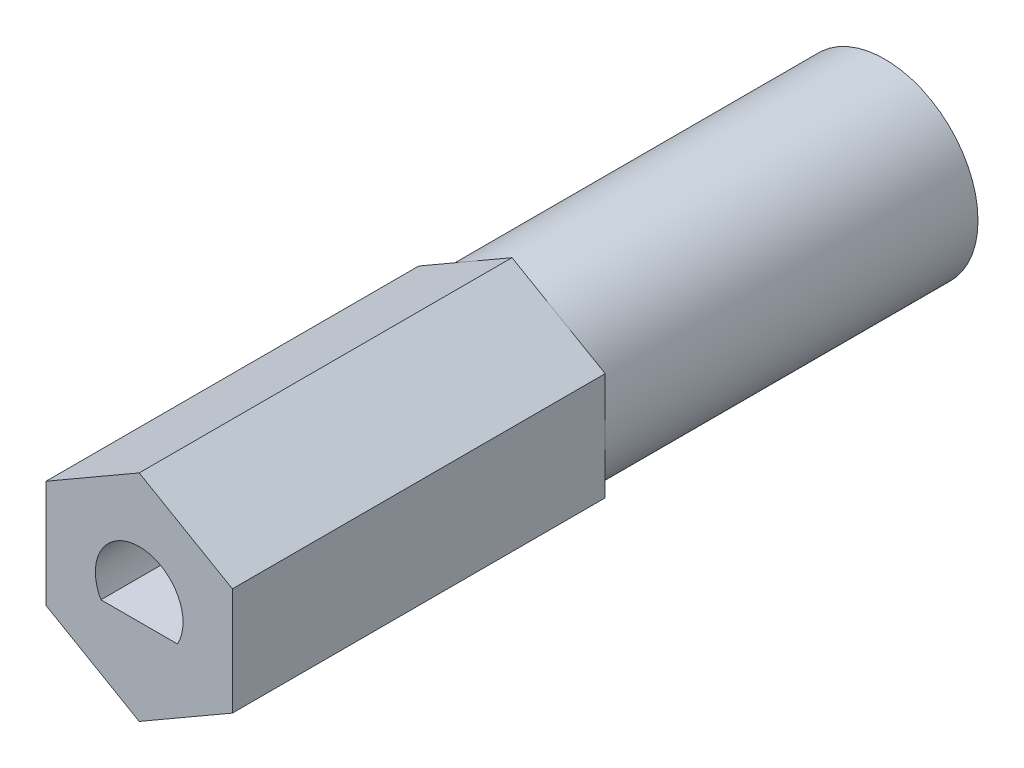
SolidWorks part; units mm, degrees
ref_plane "Front Plane" through (0, 0, 0) normal (0, 0, 1) x (1, 0, 0)
ref_plane "Top Plane" through (0, 0, 0) normal (0, 1, 0) x (1, 0, 0)
ref_plane "Right Plane" through (0, 0, 0) normal (1, 0, 0) x (0, 0, -1)
sketch "Sketch1" plane through (0, 0, 0) normal (0, 0, 1) x (1, 0, 0)
  line L1 (0, 3.6662) -> (-3.175, 1.8331)
  line L2 (-3.175, 1.8331) -> (-3.175, -1.8331)
  line L3 (-3.175, -1.8331) -> (0, -3.6662)
  line L4 (0, -3.6662) -> (3.175, -1.8331)
  line L5 (3.175, -1.8331) -> (3.175, 1.8331)
  line L6 (3.175, 1.8331) -> (0, 3.6662)
  circle A0 centre (0, 0) radius 3.175
  circle A1 centre (0, 0) radius 3.175 construction
  dimension "D1" = 6.35
extrude "Boss-Extrude1" add sketch "Sketch1" against normal blind 25.4 contours L1 L2 L3 L4 L5 L6
sketch "Sketch2" plane through (0, 0, 0) normal (0, 0, 1) x (1, 0, 0)
  line L0 (-1.3035, -0.729) -> (1.3035, -0.729)
  arc A0 (1.3035, -0.729) -> (-1.3035, -0.729) centre (0, 0) ccw
  dimension "D1" = 1.4935
  dimension "D2" = 2.2225
extrude "Cut-Extrude1" cut sketch "Sketch2" against normal blind 5.08
ref_plane "Plane1" through (0, 0, -12.7) normal (0, 0, 1) x (1, 0, 0)
sketch "Sketch3" plane through (0, 0, -12.7) normal (0, 0, 1) x (1, 0, 0)
  circle A0 centre (0, 0) radius 3.175
  dimension "D1" = 6.35
extrude "Cut-Extrude2" cut sketch "Sketch3" against normal through all flip side to cut
